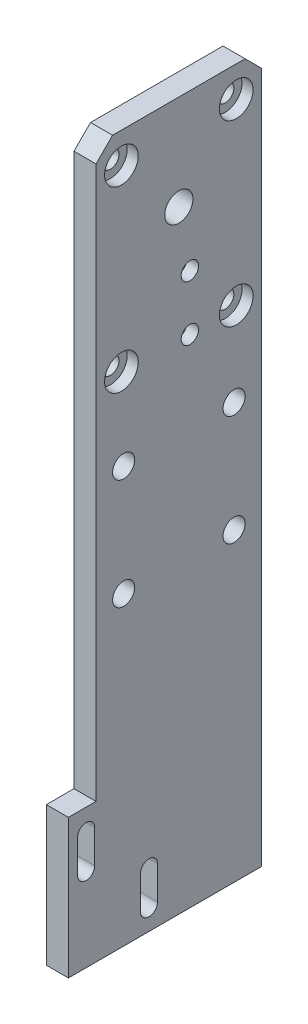
SolidWorks part; units mm, degrees
ref_plane "Alzado" through (0, 0, 0) normal (0, 0, 1) x (1, 0, 0)
ref_plane "Planta" through (0, 0, 0) normal (0, 1, 0) x (1, 0, 0)
ref_plane "Vista lateral" through (0, 0, 0) normal (1, 0, 0) x (0, 0, -1)
sketch "Croquis1" plane through (0, 0, 0) normal (1, 0, 0) x (0, 0, -1)
  line L1 (-15, -63) -> (15, -63)
  line L2 (-15, -63) -> (-15, 63)
  line L3 (-15, 63) -> (15, 63)
  line L4 (15, -63) -> (15, 63)
  line L5 (-15, -63) -> (15, 63) construction
  line L6 (-15, 63) -> (15, -63) construction
  point P0 (0, 0)
  dimension "D1" = 30
  dimension "D2" = 126
extrude "Saliente-Extruir1" add sketch "Croquis1" along normal blind 4
sketch "Croquis3" plane through (4, 0, 0) normal (1, 0, 0) x (0, 0, -1)
  line L0 (-10, 10.1) -> (10, 10.1) construction
  line L2 (15, 63) -> (-15, 63) construction
  line L4 (-10, 10.1) -> (-10, -9.9) construction
  circle A0 centre (-10, 10.1) radius 2
  circle A1 centre (10, 10.1) radius 2
  circle A2 centre (0, 10.1) radius 2 construction
  circle A3 centre (-10, -9.9) radius 2
  circle A4 centre (0, -9.9) radius 2 construction
  circle A5 centre (10, -9.9) radius 2
  dimension "D2" = 4
  dimension "D1" = 52.9
  dimension "D3" = 20
  dimension "D5" = 20
  dimension "D4" = 2
extrude "Cortar-Extruir2" cut sketch "Croquis3" against normal through all
sketch "Croquis8" plane through (0, 0, 0) normal (-1, 0, 0) x (0, 0, 1)
  line L1 (0, 45.75) -> (0, 10.1) construction
  line L2 (0, 10.1) -> (10, 10.1) construction
  circle A0 centre (0, 45.75) radius 2.55
  dimension "D2" = 5.1
  dimension "D1" = 35.65
extrude "Cortar-Extruir3" cut sketch "Croquis8" against normal through all
sketch "Croquis21" plane through (0, 0, 0) normal (-1, 0, 0) x (0, 0, 1)
  line L1 (15, -63) -> (20, -63)
  line L2 (15, -63) -> (15, -40)
  line L3 (15, -40) -> (20, -40)
  line L4 (20, -63) -> (20, -40)
  dimension "D1" = 5
  dimension "D2" = 23
extrude "Saliente-Extruir2" add sketch "Croquis21" against normal up to surface (4 mm away) up to face at (4, 45.75, 2.55)
sketch "Croquis10" plane through (4, 0, 0) normal (1, 0, 0) x (0, 0, -1)
  line L0 (-16.7909, -43.96) -> (-5.4772, -55.2737) construction
  line L1 (-15.6949, -42.864) -> (-4.3812, -54.1777)
  line L2 (-17.8869, -45.056) -> (-6.5732, -56.3697)
  line L3 (-15, 63) -> (-15, -40) construction
  line L5 (-15, -40) -> (-20, -40) construction
  line L6 (-20, -63) -> (-20, -40) construction
  arc A0 (-15.6949, -42.864) -> (-17.8869, -45.056) centre (-16.7909, -43.96) ccw
  arc A1 (-6.5732, -56.3697) -> (-4.3812, -54.1777) centre (-5.4772, -55.2737) ccw
  dimension "D1" = 3.1
  dimension "D2" = 45
  dimension "D3" = 3.2091
  dimension "D4" = 3.96
  dimension "D5" = 16
sketch "Croquis23" plane through (4, 0, 0) normal (1, 0, 0) x (0, 0, -1)
  line L0 (-16.7909, -43.96) -> (-16.7909, -49.96) construction
  line L1 (-15.2409, -43.96) -> (-15.2409, -49.96)
  line L2 (-18.3409, -43.96) -> (-18.3409, -49.96)
  line L4 (-5.4072, -55.3437) -> (-5.4072, -61.3437) construction
  line L5 (-3.8572, -55.3437) -> (-3.8572, -61.3437)
  line L6 (-6.9572, -55.3437) -> (-6.9572, -61.3437)
  arc A0 (-15.2409, -43.96) -> (-18.3409, -43.96) centre (-16.7909, -43.96) ccw
  arc A1 (-18.3409, -49.96) -> (-15.2409, -49.96) centre (-16.7909, -49.96) ccw
  arc A2 (-3.8572, -55.3437) -> (-6.9572, -55.3437) centre (-5.4072, -55.3437) ccw
  arc A3 (-6.9572, -61.3437) -> (-3.8572, -61.3437) centre (-5.4072, -61.3437) ccw
  arc A4 (-15.6949, -42.864) -> (-17.8869, -45.056) centre (-16.7909, -43.96) ccw construction
  point P3 (-16.7909, -46.96)
  point P10 (-5.4072, -58.3437)
  dimension "D1" = 6
  dimension "D2" = 0.07
  dimension "D3" = 0.07
extrude "Cortar-Extruir16" cut sketch "Croquis23" against normal through all
sketch "Croquis11" plane through (4, 0, 0) normal (1, 0, 0) x (0, 0, -1)
  line L0 (15, -63) -> (15, 63) construction
  line L2 (-10, 10.1) -> (10, 10.1) construction
  line L3 (2, 24.75) -> (2, 10.1) construction
  line L8 (2, 34.75) -> (2, 24.75) construction
  circle A4 centre (2, 34.75) radius 1.575
  circle A5 centre (2, 24.75) radius 1.575
  dimension "D1" = 13
  dimension "D3" = 3.15
  dimension "D2" = 14.65
  dimension "D4" = 10
extrude "Cortar-Extruir8" cut sketch "Croquis11" against normal through all
sketch "Croquis15" plane through (4, 0, 0) normal (1, 0, 0) x (0, 0, -1)
  line L0 (-10.4, 57.45) -> (10.4, 25.1) construction
  line L1 (-10.4, 57.45) -> (10.4, 57.45) construction
  line L2 (-10.4, 57.45) -> (-10.4, 25.1) construction
  line L3 (-10.4, 25.1) -> (10.4, 25.1) construction
  line L4 (10.4, 57.45) -> (10.4, 25.1) construction
  line L5 (0, 41.275) -> (0, 45.75) construction
  line L6 (-15.86, 54.7) -> (22.092, 54.7) construction
  line L7 (-15, 63) -> (-15, -40) construction
  line L8 (-10, 10.1) -> (10, 10.1) construction
  line L9 (10, 10.1) -> (10, 20.1) construction
  line L10 (10, 20.1) -> (-10, 20.1) construction
  line L11 (-11.975, 57.45) -> (-11.975, 70.4928) construction
  line L13 (-23.8132, 53.7) -> (25.052, 53.7) construction
  line L14 (-10.4, 59.025) -> (-6.2662, 59.025) construction
  circle A0 centre (-10.4, 57.45) radius 1.575
  circle A1 centre (10.4, 57.45) radius 1.575
  circle A2 centre (-10.4, 25.1) radius 1.575
  circle A3 centre (10.4, 25.1) radius 1.575
  circle A4 centre (0, 45.75) radius 7.95 construction
  circle A5 centre (-10.4, 57.45) radius 1.5 construction
  circle A6 centre (-10.4, 57.45) radius 2.75 construction
  circle A9 centre (0, 45.75) radius 6 construction
  dimension "D1" = 3.15
  dimension "D2" = 15.9
  dimension "D3" = 3
  dimension "D8" = 1
  dimension "D4" = 12
  dimension "D10" = 5.5
  dimension "D5" = 4.6
  dimension "D6" = 10
  dimension "D7" = 5
extrude "Cortar-Extruir11" cut sketch "Croquis15" against normal through all
chamfer "Chaflán2" distance 3 angle 45 2 edges at (2, 63, -15) (2, 63, 15)
sketch "Croquis19" plane through (0, 0, 0) normal (-1, 0, 0) x (0, 0, 1)
  circle A0 centre (-2, 24.75) radius 3.5
  circle A1 centre (-2, 34.75) radius 3.5
  dimension "D1" = 7
extrude "Cortar-Extruir13" cut sketch "Croquis19" against normal blind 1.9
sketch "Croquis20" plane through (4, 0, 0) normal (1, 0, 0) x (0, 0, -1)
  circle A0 centre (-10.4, 57.45) radius 3.05
  circle A1 centre (10.4, 57.45) radius 3.05
  circle A2 centre (10.4, 25.1) radius 3.05
  circle A3 centre (-10.4, 25.1) radius 3.05
  dimension "D1" = 6.1
extrude "Cortar-Extruir14" cut sketch "Croquis20" against normal blind 2
sketch "Croquis24" plane through (4, 0, 0) normal (1, 0, 0) x (0, 0, -1)
  line L0 (-16.7909, -43.96) -> (-16.7909, -40) construction
  line L1 (-20, -63) -> (15, -63)
  line L2 (-20, -63) -> (-20, -65.2)
  line L3 (-20, -65.2) -> (15, -65.2)
  line L4 (15, -63) -> (15, -65.2)
  line L5 (-15, -40) -> (-20, -40) construction
  dimension "D1" = 2.2
extrude "Saliente-Extruir3" add sketch "Croquis24" against normal up to surface (4 mm away) up to face at (0, 34.75, 1.5)
